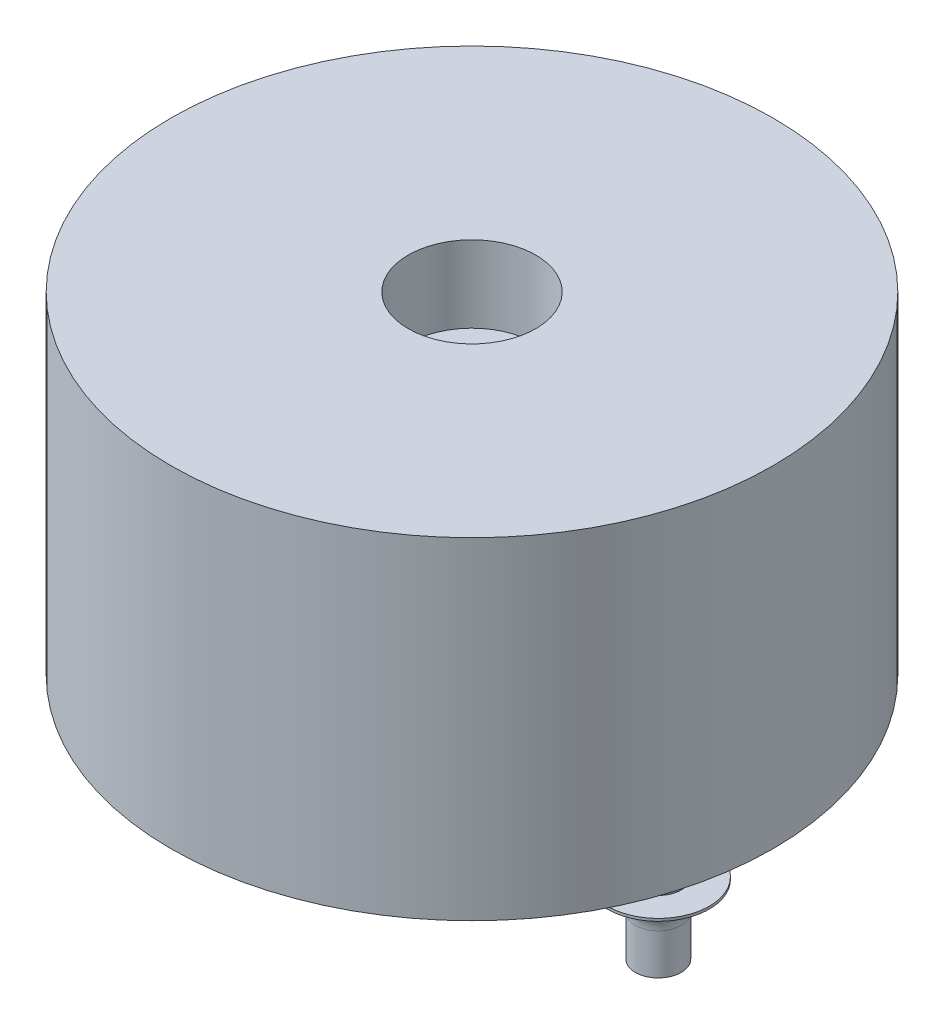
SolidWorks part; units mm, degrees
ref_plane "Plan de face" through (0, 0, 0) normal (0, 0, 1) x (1, 0, 0)
ref_plane "Plan de dessus" through (0, 0, 0) normal (0, 1, 0) x (1, 0, 0)
ref_plane "Plan de droite" through (0, 0, 0) normal (1, 0, 0) x (0, 0, -1)
sketch "Esquisse1" plane through (0, 0, 0) normal (0, 1, 0) x (1, 0, 0)
  circle A0 centre (0, 0) radius 5.9
  dimension "D1" = 11.8
extrude "Boss.-Extru.1" add sketch "Esquisse1" along normal blind 6.5
sketch "Esquisse2" plane through (0, 6.5, 0) normal (0, 1, 0) x (1, 0, 0)
  circle A0 centre (0, 0) radius 1.25
  dimension "D1" = 2.5
extrude "Enlèv. mat.-Extru.1" cut sketch "Esquisse2" against normal blind 1.5
sketch "Esquisse4" plane through (0, 0, 0) normal (0, 0, 1) x (1, 0, 0)
  line L0 (-3.65, 0) -> (-3.65, -3) construction
  line L1 (-5.9, 0) -> (5.9, 0) construction
  line L2 (-3.65, -3) -> (-4.1, -3)
  line L3 (-4.1, -3) -> (-4.1, -2.2)
  line L4 (-3.65, 0) -> (-3.65, -3)
  line L6 (-4.1, 0) -> (-3.65, 0)
  line L7 (-4.1, 0) -> (-4.1, -1.6)
  line L8 (-4.1, -1.6) -> (-4.65, -1.6)
  line L9 (-4.65, -1.6) -> (-4.65, -1.65)
  arc A0 (-4.1, -2.2) -> (-4.65, -1.65) centre (-4.65, -2.2) ccw
  dimension "D1" = 3.65
  dimension "D2" = 0.45
  dimension "D3" = 1
  dimension "D4" = 0.05
  dimension "D5" = 1.6
  dimension "D6" = 3
revolve "Révolution1" add sketch "Esquisse4" angle 360 about L0
pattern_linear "Répétition linéaire1" count 2 spacing 7.3 along (1, 0, 0) of "Révolution1"
